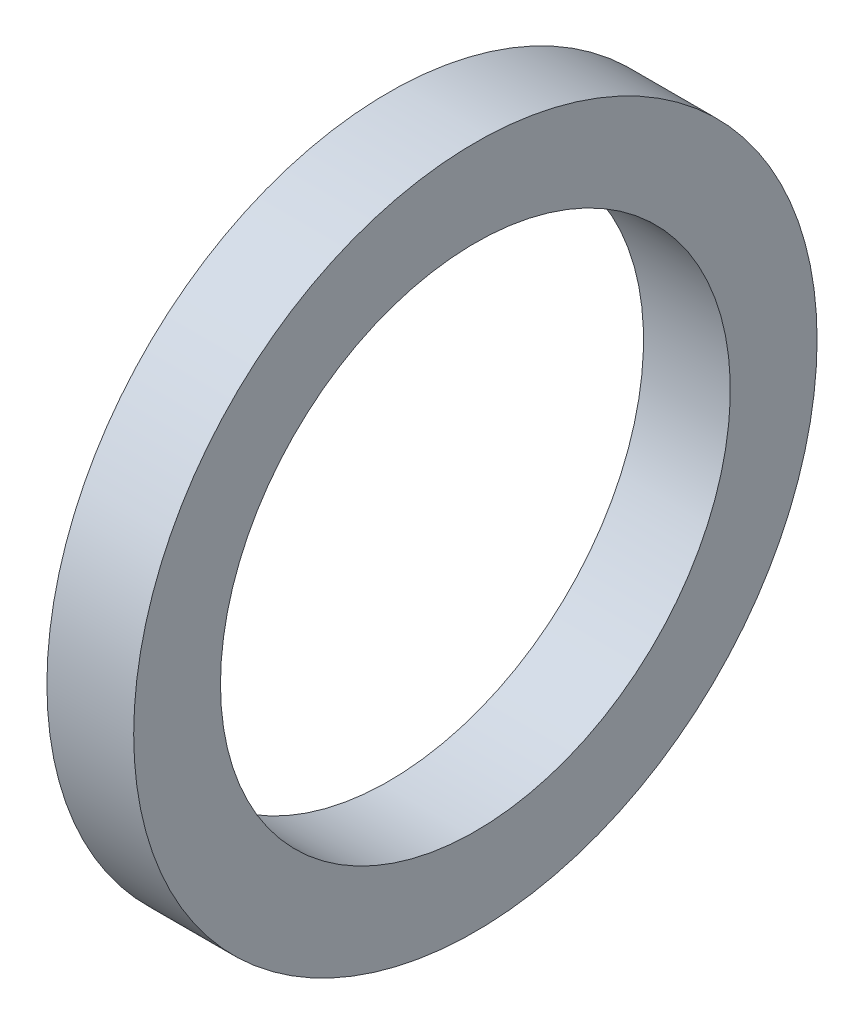
SolidWorks part; units mm, degrees
ref_plane "Front Plane" through (0, 0, 0) normal (0, 0, 1) x (1, 0, 0)
ref_plane "Top Plane" through (0, 0, 0) normal (0, 1, 0) x (1, 0, 0)
ref_plane "Right Plane" through (0, 0, 0) normal (1, 0, 0) x (0, 0, -1)
sketch "Sketch1" plane through (0, 0, 0) normal (0, 0, 1) x (1, 0, 0)
  line L0 (-43.7166, 0) -> (79.6876, 0) construction
  line L2 (0, -5.969) -> (2.032, -5.969)
  line L3 (0, -5.969) -> (0, -8.001)
  line L4 (0, -8.001) -> (2.032, -8.001)
  line L5 (2.032, -5.969) -> (2.032, -8.001)
  dimension "A" = 11.938
  dimension "B" = 16.002
  dimension "C" = 2.032
revolve "Revolve1" add sketch "Sketch1" angle 360 about L0
sketch "Sketch2" [suppressed] plane through (0, 0, 0) normal (0, 0, 1) x (1, 0, 0)
  line L0 (-34.685, 0) -> (47.6686, 0) construction
  circle A0 centre (2.54, -5.715) radius 0.762
  dimension "D1" = 2.54
  dimension "E" = 1.524
  dimension "D" = 9.906
revolve "Revolve3" [suppressed] add sketch "Sketch2" angle 360 about L0
